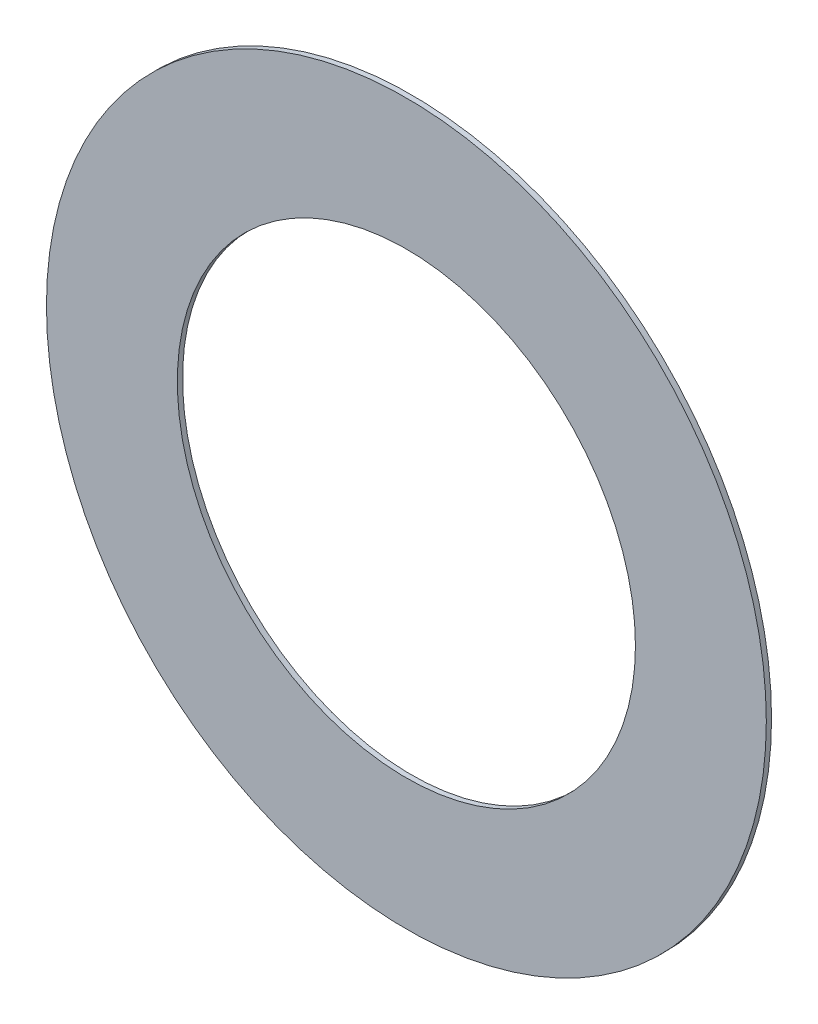
SolidWorks part; units mm, degrees
material "AISI 1020"
ref_plane "Front Plane" through (0, 0, 0) normal (0, 0, 1) x (1, 0, 0)
ref_plane "Top Plane" through (0, 0, 0) normal (0, 1, 0) x (1, 0, 0)
ref_plane "Right Plane" through (0, 0, 0) normal (1, 0, 0) x (0, 0, -1)
sketch "Sketch1" plane through (0, 0, 0) normal (0, 0, 1) x (1, 0, 0)
  circle A0 centre (0, 0) radius 11.1125
  circle A1 centre (0, 0) radius 17.4625
  dimension "D1" = 22.225
  dimension "D2" = 34.925
extrude "Boss-Extrude1" add sketch "Sketch1" along normal blind 0.254
